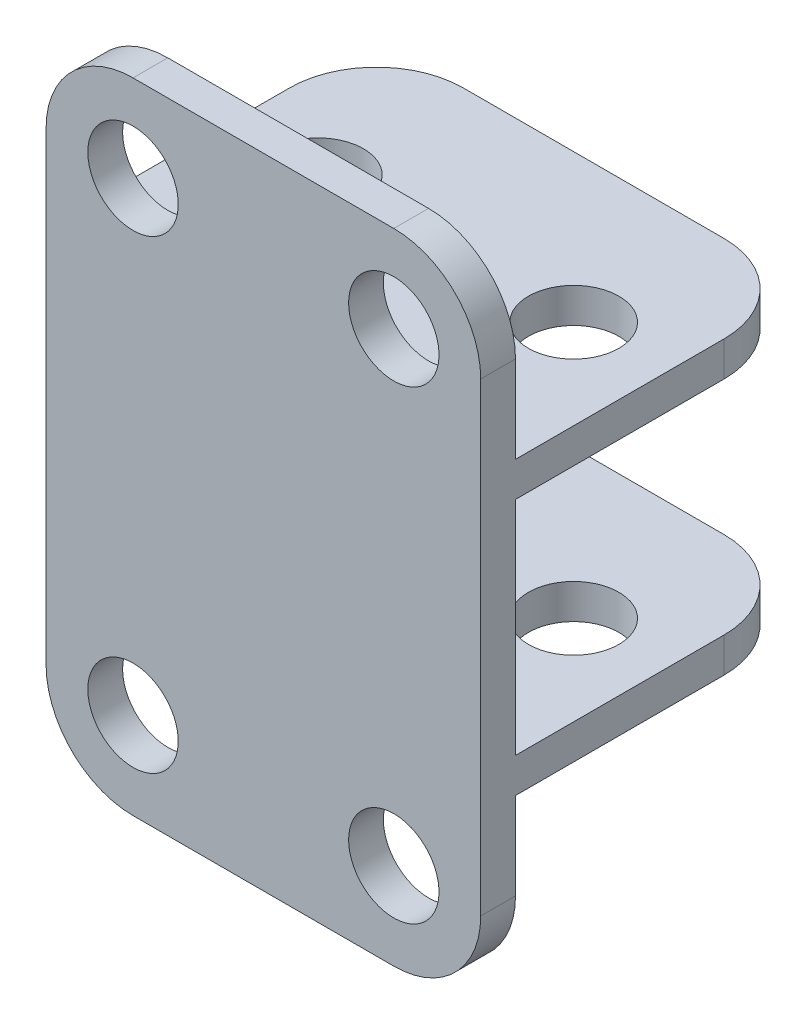
SolidWorks part; units mm, degrees
ref_plane "Front Plane" through (0, 0, 0) normal (0, 0, 1) x (1, 0, 0)
ref_plane "Top Plane" through (0, 0, 0) normal (0, 1, 0) x (1, 0, 0)
ref_plane "Right Plane" through (0, 0, 0) normal (1, 0, 0) x (0, 0, -1)
sketch "Sketch1" plane through (0, 0, 0) normal (0, 1, 0) x (1, 0, 0)
  line L0 (-7.345, 0) -> (7.345, 0) construction
  line L1 (12.5, -8.5) -> (-12.5, -8.5)
  line L2 (12.5, -8.5) -> (12.5, 8.5)
  line L3 (12.5, 8.5) -> (-12.5, 8.5)
  line L4 (-12.5, -8.5) -> (-12.5, 8.5)
  line L5 (12.5, -8.5) -> (-12.5, 8.5) construction
  line L6 (12.5, 8.5) -> (-12.5, -8.5) construction
  circle A0 centre (-7.345, 0) radius 2.6
  circle A1 centre (7.345, 0) radius 2.6
  point P0 (0, 0)
  point P8 (0, 0)
  dimension "D4" = 5.2
  dimension "D5" = 5.2
  dimension "D1" = 25
  dimension "D2" = 17
  dimension "D3" = 14.69
extrude "Boss-Extrude1" add sketch "Sketch1" along normal blind 2
sketch "Sketch2" plane through (0, 0, 8.5) normal (0, 0, 1) x (1, 0, 0)
  line L0 (-12.5, 2) -> (12.5, 2) construction
  line L1 (-12.5, 0) -> (12.5, 0)
  line L2 (-12.5, 0) -> (-12.5, 14.75)
  line L3 (-12.5, 14.75) -> (12.5, 14.75)
  line L4 (12.5, 0) -> (12.5, 14.75)
  dimension "D1" = 12.75
extrude "Boss-Extrude2" add sketch "Sketch2" along normal blind 2
ref_plane "Plane1" through (0, 8.375, 0) normal (0, 1, 0) x (1, 0, 0)
mirror "Mirror2" about plane through (0, 8.375, 0) normal (0, 1, 0) of bodies 102
sketch "Sketch3" plane through (0, 16.75, 0) normal (0, 1, 0) x (1, 0, 0)
  line L0 (12.5, -10.5) -> (12.5, 8.5) construction
  line L1 (-12.5, -10.5) -> (12.5, -10.5)
  line L2 (-12.5, -10.5) -> (-12.5, -8.5)
  line L3 (-12.5, -8.5) -> (12.5, -8.5)
  line L4 (12.5, -10.5) -> (12.5, -8.5)
  dimension "D1" = 2
extrude "Boss-Extrude3" add sketch "Sketch3" along normal blind 10
mirror "Mirror3" about plane through (0, 8.375, 0) normal (0, 1, 0) of bodies 105
fillet "Fillet1" radius 5 8 edges at (12.5, 15.75, -8.5) (-12.5, 15.75, -8.5) (-12.5, 1, -8.5) (12.5, 1, -8.5) (12.5, -10, 9.5) (-12.5, -10, 9.5) (12.5, 26.75, 9.5) (-12.5, 26.75, 9.5)
sketch "Sketch4" plane through (0, 0, 8.5) normal (0, 0, -1) x (-1, 0, 0)
  line L0 (0, 21.75) -> (-7.5, 21.75) construction
  line L1 (0, 23.9513) -> (0, 18.5036) construction
  line L2 (12.5, 14.75) -> (-12.5, 14.75) construction
  line L3 (55, 8.375) -> (-55, 8.375) construction
  circle A0 centre (-7.5, 21.75) radius 2.6
  circle A1 centre (7.5, 21.75) radius 2.6
  circle A2 centre (7.5, -5) radius 2.6
  circle A3 centre (-7.5, -5) radius 2.6
  dimension "D1" = 5.2
  dimension "D2" = 7
extrude "Cut-Extrude1" cut sketch "Sketch4" against normal blind 10
equation "\"14ز5\"=17.3015"
